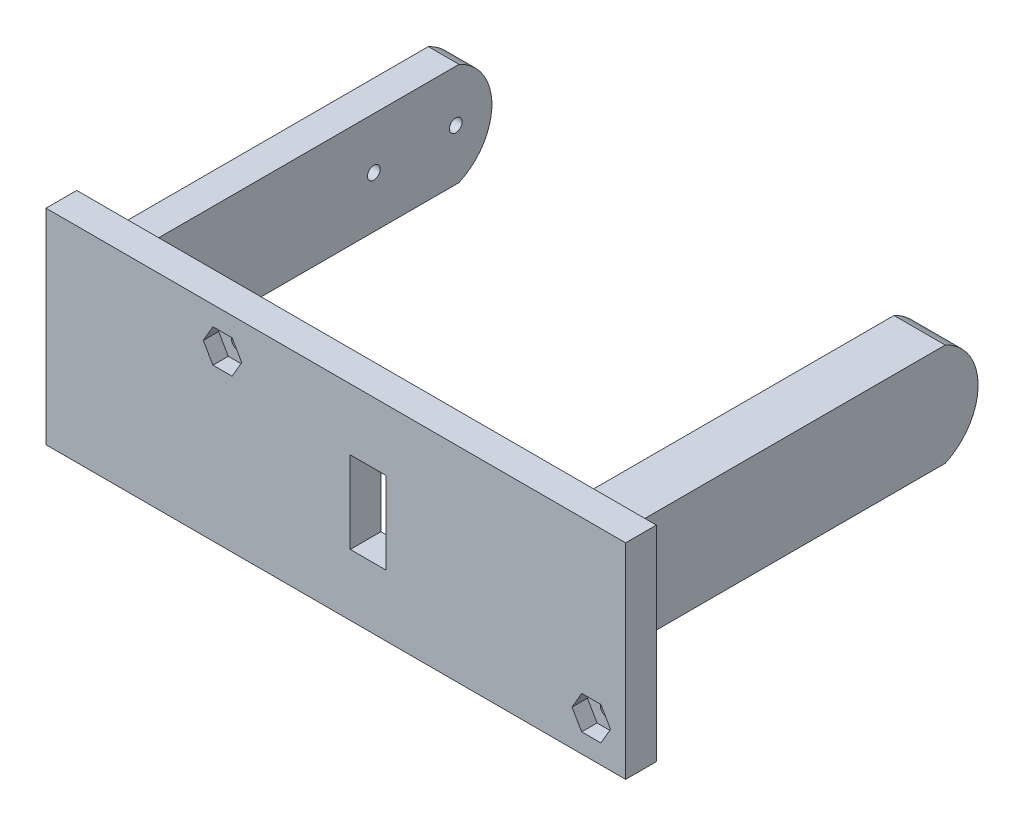
SolidWorks part; units mm, degrees
ref_plane "Front Plane" through (0, 0, 0) normal (0, 0, 1) x (1, 0, 0)
ref_plane "Top Plane" through (0, 0, 0) normal (0, 1, 0) x (1, 0, 0)
ref_plane "Right Plane" through (0, 0, 0) normal (1, 0, 0) x (0, 0, -1)
sketch "Sketch1" plane through (0, 0, 0) normal (0, 1, 0) x (1, 0, 0)
  line L0 (0, 0) -> (0, -101.6)
  line L1 (0, -101.6) -> (107.8484, -101.6)
  line L2 (107.8484, -101.6) -> (107.8484, 0)
  line L3 (107.8484, 0) -> (120.5484, 0)
  line L4 (120.5484, 0) -> (120.5484, -109.22)
  line L5 (120.5484, -109.22) -> (-7.62, -109.22)
  line L6 (-7.62, -109.22) -> (-7.62, 0)
  line L7 (-7.62, 0) -> (0, 0)
  dimension "D1" = 107.8484
  dimension "D2" = 7.62
  dimension "D3" = 12.7
  dimension "D4" = 7.62
  dimension "D5" = 101.6
extrude "Boss-Extrude1" add sketch "Sketch1" along normal blind 25.4
sketch "Sketch2" plane through (0, 0, 0) normal (1, 0, 0) x (0, 0, -1)
  line L0 (0, 25.4) -> (0, 0) construction
  circle A0 centre (-25.4, 12.7) radius 3.175
  circle A2 centre (-15.24, 12.7) radius 1.5875
  circle A3 centre (-35.56, 12.7) radius 1.5875
  point P4 (0, 12.7)
  dimension "D1" = 6.35
  dimension "D3" = 3.175
  dimension "D7" = 10.16
  dimension "D8" = 3.175
  dimension "D2" = 25.4
  dimension "D5" = 10.16
sketch "Sketch4" plane through (107.8484, 0, 0) normal (-1, 0, 0) x (0, 0, 1)
  line L0 (0, 25.4) -> (0, 0) construction
  circle A0 centre (25.4, 12.7) radius 3.302
  point P4 (0, 12.7)
  dimension "D1" = 25.4
  dimension "D2" = 6.604
extrude "Cut-Extrude2" cut sketch "Sketch4" against normal blind 7.62 contours A0
extrude "Cut-Extrude3" cut sketch "Sketch2" against normal blind 7.62
sketch "Sketch6" plane through (0, 0, 109.22) normal (0, 0, 1) x (1, 0, 0)
  line L0 (-7.62, 25.4) -> (120.5484, 25.4) construction
  line L1 (-7.62, 25.4) -> (120.5484, 25.4)
  line L2 (-7.62, 25.4) -> (-7.62, 38.1)
  line L3 (-7.62, 38.1) -> (120.5484, 38.1)
  line L4 (120.5484, 25.4) -> (120.5484, 38.1)
  line L5 (-7.62, 0) -> (120.5484, 0) construction
  line L6 (-7.62, 0) -> (120.5484, 0)
  line L7 (-7.62, 0) -> (-7.62, -12.7)
  line L8 (-7.62, -12.7) -> (120.5484, -12.7)
  line L9 (120.5484, 0) -> (120.5484, -12.7)
  line L10 (-7.62, 25.4) -> (-7.62, 0) construction
  line L11 (120.5484, 25.4) -> (120.5484, 0) construction
  point P13 (56.4642, 25.4)
  point P14 (56.4642, 0)
  dimension "D1" = 50.8
extrude "Boss-Extrude2" add sketch "Sketch6" against normal up to surface (7.62 mm away) up to face at (53.9242, 12.7, 101.6)
sketch "Sketch9" plane through (0, 0, 109.22) normal (0, 0, 1) x (1, 0, 0)
  line L1 (120.5484, 38.1) -> (136.0989, 38.1)
  line L2 (120.5484, 38.1) -> (120.5484, -12.7)
  line L3 (120.5484, -12.7) -> (136.0989, -12.7)
  line L4 (136.0989, 38.1) -> (136.0989, -12.7)
extrude "Boss-Extrude3" add sketch "Sketch9" against normal up to surface (7.62 mm away) up to face at (55.6175, 12.7, 101.6)
sketch "Sketch7" plane through (0, 0, 109.22) normal (0, 0, 1) x (1, 0, 0)
  line L0 (-7.62, 38.1) -> (-7.62, -12.7) construction
  line L1 (40.9102, 29.21) -> (38.5272, 33.3375)
  line L2 (38.5272, 33.3375) -> (33.7612, 33.3375)
  line L3 (33.7612, 33.3375) -> (31.3782, 29.21)
  line L4 (31.3782, 29.21) -> (33.7612, 25.0825)
  line L5 (33.7612, 25.0825) -> (38.5272, 25.0825)
  line L6 (38.5272, 25.0825) -> (40.9102, 29.21)
  line L7 (132.3502, -3.81) -> (129.9672, 0.3175)
  line L8 (129.9672, 0.3175) -> (125.2012, 0.3175)
  line L9 (125.2012, 0.3175) -> (122.8182, -3.81)
  line L10 (122.8182, -3.81) -> (125.2012, -7.9375)
  line L11 (125.2012, -7.9375) -> (129.9672, -7.9375)
  line L12 (129.9672, -7.9375) -> (132.3502, -3.81)
  line L15 (-7.62, 25.4) -> (-7.62, 38.1) construction
  circle A2 centre (36.1442, 29.21) radius 4.1275 construction
  circle A3 centre (127.5842, -3.81) radius 4.1275 construction
  point P21 (-7.62, 12.7)
  dimension "D1" = 8.255
  dimension "D2" = 8.255
  dimension "D3" = 16.51
  dimension "D4" = 33.02
  dimension "D5" = 91.44
  dimension "D6" = 43.7642
extrude "Cut-Extrude4" cut sketch "Sketch7" against normal blind 3.81
sketch "Sketch8" plane through (0, 0, 109.22) normal (0, 0, 1) x (1, 0, 0)
  circle A0 centre (36.1442, 29.21) radius 4.1275
  circle A1 centre (127.5842, -3.81) radius 4.1275
  dimension "D1" = 8.255
  dimension "D2" = 8.255
sketch "Sketch10" plane through (-7.62, 0, 0) normal (-1, 0, 0) x (0, 0, 1)
  circle A1 centre (15.24, 12.7) radius 2.921
  circle A2 centre (35.56, 12.7) radius 2.921
  dimension "D1" = 5.842
  dimension "D2" = 5.842
extrude "Cut-Extrude5" cut sketch "Sketch10" against normal blind 3.048
sketch "Sketch11" plane through (0, 0, 105.41) normal (0, 0, 1) x (1, 0, 0)
  circle A0 centre (36.1442, 29.21) radius 1.5875
  circle A1 centre (127.5842, -3.81) radius 1.5875
  dimension "D1" = 3.175
  dimension "D2" = 3.175
extrude "Cut-Extrude6" cut sketch "Sketch11" against normal through all
sketch "Sketch12" plane through (0, 0, 109.22) normal (0, 0, 1) x (1, 0, 0)
  line L0 (-7.62, -12.7) -> (136.0989, -12.7) construction
  line L1 (76.708, 22.86) -> (67.818, 22.86)
  line L2 (76.708, 22.86) -> (76.708, 2.54)
  line L3 (76.708, 2.54) -> (67.818, 2.54)
  line L4 (67.818, 22.86) -> (67.818, 2.54)
  line L6 (-7.62, 25.4) -> (-7.62, 38.1) construction
  dimension "D1" = 15.24
  dimension "D2" = 75.438
  dimension "D3" = 8.89
  dimension "D4" = 20.32
extrude "Cut-Extrude7" cut sketch "Sketch12" against normal up to next
sketch "Sketch13" plane through (-7.62, 0, 0) normal (-1, 0, 0) x (0, 0, 1)
  circle A0 centre (25.4, 12.7) radius 3.175
extrude "Boss-Extrude4" add sketch "Sketch13" against normal up to surface (7.62 mm away) up to face at (0, 12.7, 13.6525)
sketch "Sketch14" plane through (-7.62, 0, 0) normal (-1, 0, 0) x (0, 0, 1)
  line L0 (0, 25.4) -> (101.6, 25.4) construction
  line L1 (0, 0) -> (101.6, 0) construction
  line L2 (14.4264, 25.4) -> (0, 25.4)
  line L3 (0, 25.4) -> (0, 0)
  line L4 (0, 0) -> (14.4264, 0)
  arc A0 (14.4264, 25.4) -> (14.4264, 0) centre (20.2462, 12.7) ccw
  dimension "D1" = 13.97
extrude "Cut-Extrude8" cut sketch "Sketch14" against normal through all both and the other way through all
